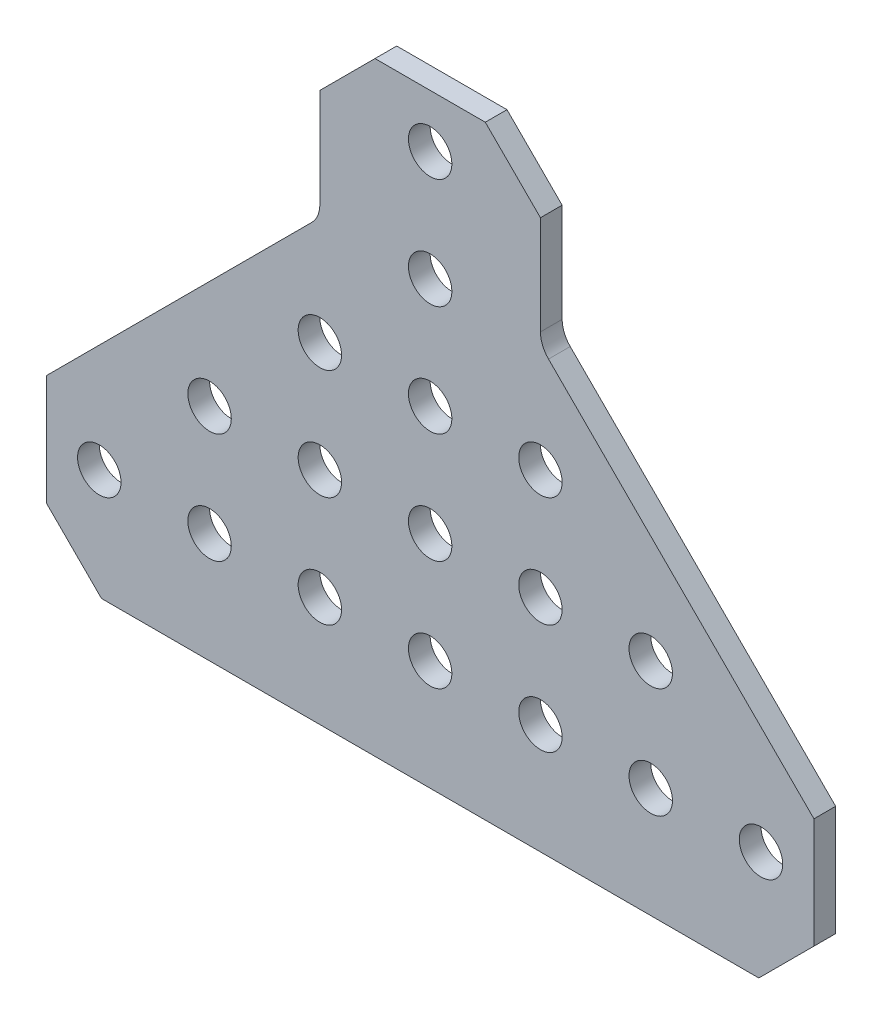
SolidWorks part; units mm, degrees
material "5052-H32"
ref_plane "Front Plane" through (0, 0, 0) normal (0, 0, 1) x (1, 0, 0)
ref_plane "Top Plane" through (0, 0, 0) normal (0, 1, 0) x (1, 0, 0)
ref_plane "Right Plane" through (0, 0, 0) normal (1, 0, 0) x (0, 0, -1)
ref_plane "Plane1" through (0, 0, -1.25) normal (0, 0, -1) x (-1, 0, 0)
sketch "Sketch1" plane through (0, 0, -1.25) normal (0, 0, -1) x (-1, 0, 0)
  line L0 (44.196, 6.35) -> (13.6299, 36.9161)
  line L1 (12.7, 39.1611) -> (12.7, 50.546)
  line L2 (12.7, 50.546) -> (6.35, 56.896)
  line L3 (6.35, 56.896) -> (-6.35, 56.896)
  line L4 (-6.35, 56.896) -> (-12.7, 50.546)
  line L5 (-12.7, 50.546) -> (-12.7, 39.1611)
  line L6 (-13.6299, 36.9161) -> (-44.196, 6.35)
  line L7 (-44.196, 6.35) -> (-44.196, -6.35)
  line L8 (-44.196, -6.35) -> (-37.846, -12.7)
  line L9 (-37.846, -12.7) -> (37.846, -12.7)
  line L10 (37.846, -12.7) -> (44.196, -6.35)
  line L11 (44.196, -6.35) -> (44.196, 6.35)
  circle A0 centre (0, 50.8) radius 2.5
  circle A1 centre (0, 38.1) radius 2.5
  circle A2 centre (-38.1, 0) radius 2.5
  circle A3 centre (-25.4, 0) radius 2.5
  circle A4 centre (-12.7, 0) radius 2.5
  circle A5 centre (0, 0) radius 2.5
  circle A6 centre (12.7, 0) radius 2.5
  circle A7 centre (38.1, 0) radius 2.5
  circle A8 centre (25.4, 0) radius 2.5
  circle A9 centre (0, 12.7) radius 2.5
  circle A10 centre (0, 25.4) radius 2.5
  circle A11 centre (25.4, 12.7) radius 2.5
  circle A12 centre (12.7, 12.7) radius 2.5
  circle A13 centre (12.7, 25.4) radius 2.5
  circle A14 centre (-12.7, 12.7) radius 2.5
  circle A15 centre (-12.7, 25.4) radius 2.5
  circle A16 centre (-25.4, 12.7) radius 2.5
  arc A17 (13.6299, 36.9161) -> (12.7, 39.1611) centre (15.875, 39.1611) cw
  arc A18 (-12.7, 39.1611) -> (-13.6299, 36.9161) centre (-15.875, 39.1611) cw
  point P50 (0, 0)
  dimension "D1" = 5
  dimension "D2" = 5
  dimension "D3" = 5
  dimension "D4" = 5
  dimension "D5" = 5
  dimension "D6" = 5
  dimension "D7" = 5
  dimension "D8" = 5
  dimension "D9" = 5
  dimension "D10" = 5
  dimension "D11" = 5
  dimension "D12" = 5
  dimension "D13" = 5
  dimension "D14" = 5
  dimension "D15" = 5
  dimension "D16" = 5
  dimension "D17" = 5
  dimension "D18" = 3.175
  dimension "D19" = 3.175
  dimension "D20" = 6.096
  dimension "D21" = 6.35
  dimension "D22" = 18.796
  dimension "D23" = 28.321
  dimension "D24" = 30.5661
  dimension "D25" = 37.846
  dimension "D26" = 44.196
  dimension "D27" = 50.546
  dimension "D28" = 56.896
  dimension "D29" = 69.596
  dimension "D30" = 82.042
  dimension "D31" = 82.296
  dimension "D32" = 6.096
  dimension "D33" = 6.35
  dimension "D34" = 17.7349
  dimension "D35" = 18.796
  dimension "D36" = 31.496
  dimension "D37" = 44.196
  dimension "D38" = 56.896
  dimension "D39" = 69.596
  dimension "D41" = 63.246
extrude "Boss-Extrude1" add sketch "Sketch1" against normal blind 2.5
